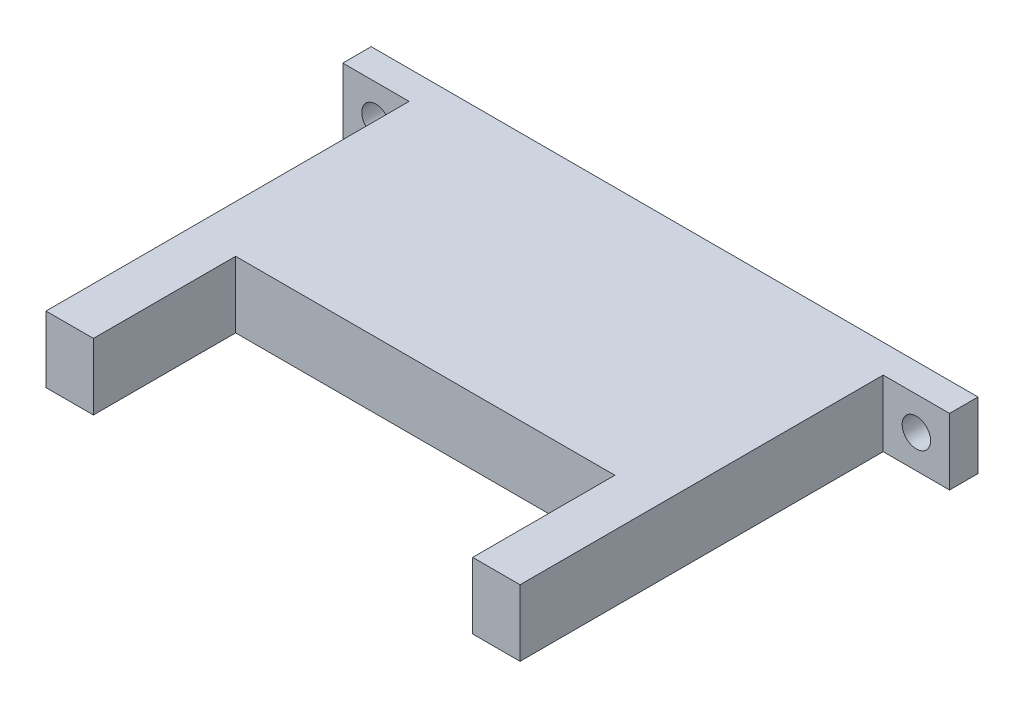
SolidWorks part; units mm, degrees
ref_plane "Front" through (0, 0, 0) normal (0, 0, 1) x (1, 0, 0)
ref_plane "Top" through (0, 0, 0) normal (0, 1, 0) x (1, 0, 0)
ref_plane "Right" through (0, 0, 0) normal (1, 0, 0) x (0, 0, -1)
sketch "Эскиз1" plane through (0, 0, 0) normal (0, 0, 1) x (1, 0, 0)
  line L1 (-32, 3.5) -> (32, 3.5)
  line L2 (-32, 3.5) -> (-32, -3.5)
  line L3 (-32, -3.5) -> (32, -3.5)
  line L4 (32, 3.5) -> (32, -3.5)
  line L5 (-32, 3.5) -> (32, -3.5) construction
  line L6 (-32, -3.5) -> (32, 3.5) construction
  point P0 (0, 0)
  dimension "D1" = 7
  dimension "D2" = 64
extrude "Бобышка-Вытянуть3" add sketch "Эскиз1" along normal blind 3
sketch "Эскиз3" plane through (0, 0, 3) normal (0, 0, 1) x (1, 0, 0)
  line L0 (32, 3.5) -> (-32, 3.5) construction
  line L1 (-25, 3.5) -> (25, 3.5)
  line L2 (-25, 3.5) -> (-25, -3.5)
  line L3 (-25, -3.5) -> (25, -3.5)
  line L4 (25, 3.5) -> (25, -3.5)
  line L5 (-32, -3.5) -> (32, -3.5) construction
  line L6 (-32, 3.5) -> (-32, -3.5) construction
  line L7 (32, -3.5) -> (32, 3.5) construction
  dimension "D1" = 7
  dimension "D2" = 7
extrude "Бобышка-Вытянуть4" add sketch "Эскиз3" along normal blind 23.3
sketch "Эскиз4" plane through (0, 0, 26.3) normal (0, 0, 1) x (1, 0, 0)
  line L0 (25, 3.5) -> (-25, 3.5) construction
  line L1 (-25, -3.5) -> (-20, -3.5)
  line L2 (-25, -3.5) -> (-25, 3.5)
  line L3 (-25, 3.5) -> (-20, 3.5)
  line L4 (-20, -3.5) -> (-20, 3.5)
  dimension "D1" = 5
extrude "Бобышка-Вытянуть5" add sketch "Эскиз4" along normal blind 15
sketch "Эскиз5" plane through (0, 0, 26.3) normal (0, 0, 1) x (1, 0, 0)
  line L0 (25, 3.5) -> (-20, 3.5) construction
  line L1 (25, -3.5) -> (20, -3.5)
  line L2 (25, -3.5) -> (25, 3.5)
  line L3 (25, 3.5) -> (20, 3.5)
  line L4 (20, -3.5) -> (20, 3.5)
  dimension "D1" = 5
extrude "Бобышка-Вытянуть6" add sketch "Эскиз5" along normal blind 15
sketch "Эскиз6" plane through (0, 0, 3) normal (0, 0, 1) x (1, 0, 0)
  line L0 (-25, 3.5) -> (-32, 3.5) construction
  line L1 (-32, 3.5) -> (-32, -3.5) construction
  circle A0 centre (-28.5, 0) radius 1.5
  dimension "D1" = 3
  dimension "D2" = 3.5
  dimension "D3" = 3.5
extrude "Вырез-Вытянуть1" cut sketch "Эскиз6" against normal blind 3
sketch "Эскиз7" plane through (0, 0, 3) normal (0, 0, 1) x (1, 0, 0)
  line L0 (32, 3.5) -> (25, 3.5) construction
  line L1 (32, -3.5) -> (32, 3.5) construction
  circle A0 centre (28.5, 0) radius 1.5
  dimension "D1" = 3
  dimension "D2" = 3.5
  dimension "D3" = 3.5
extrude "Вырез-Вытянуть2" cut sketch "Эскиз7" against normal blind 3
